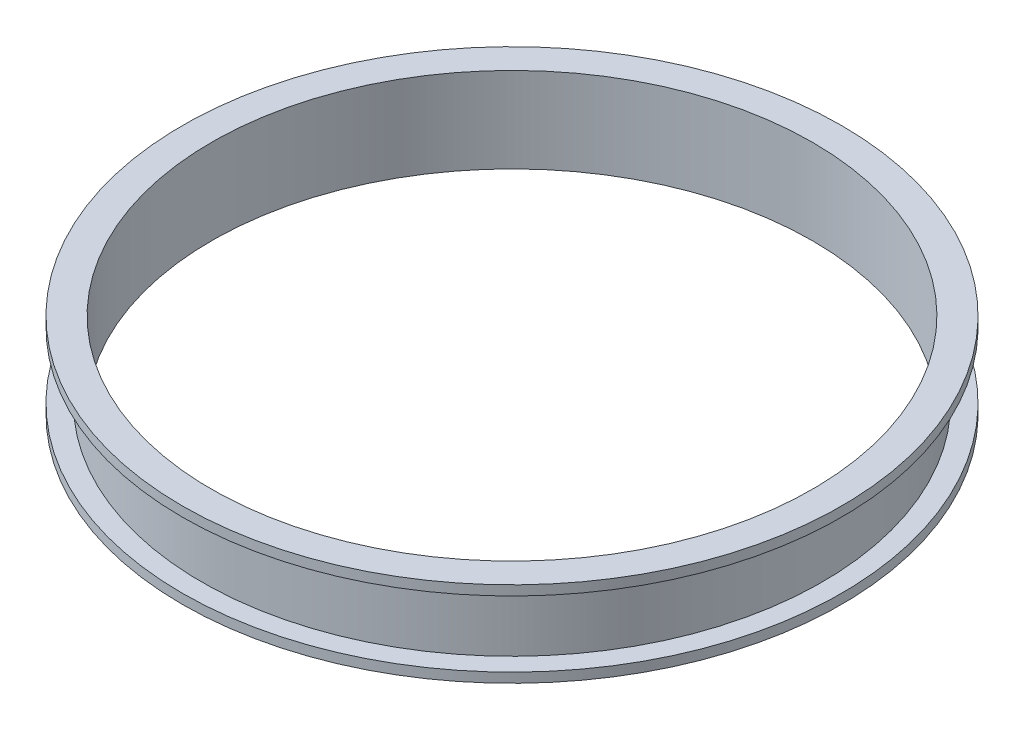
SolidWorks part; units mm, degrees
ref_plane "Front Plane" through (0, 0, 0) normal (0, 0, 1) x (1, 0, 0)
ref_plane "Top Plane" through (0, 0, 0) normal (0, 1, 0) x (1, 0, 0)
ref_plane "Right Plane" through (0, 0, 0) normal (1, 0, 0) x (0, 0, -1)
sketch "Sketch1" plane through (0, 0, 0) normal (0, 0, 1) x (1, 0, 0)
  line L0 (0, 0) -> (77.5, 0)
  line L1 (77.5, 0) -> (77.5, 19.5)
  line L2 (77.5, 19.5) -> (85, 19.5)
  line L3 (85, 19.5) -> (85, 17)
  line L4 (85, 17) -> (80, 17)
  line L5 (80, 17) -> (80, 0)
  line L6 (80, 0) -> (85, 0)
  line L7 (85, 0) -> (85, -2.5)
  line L8 (85, -2.5) -> (0, -2.5)
  line L9 (0, -2.5) -> (0, 0)
  dimension "D1" = 2.5
  dimension "D2" = 2.5
  dimension "D3" = 2.5
  dimension "D4" = 5
  dimension "D5" = 5
  dimension "D6" = 77.5
  dimension "D7" = 17
revolve "Revolve1" add sketch "Sketch1" angle 360 about L9
sketch "Sketch2" plane through (0, 0, 0) normal (0, 1, 0) x (1, 0, 0)
  circle A0 centre (0, 0) radius 77.5
  dimension "D1" = 155
extrude "Cut-Extrude1" cut sketch "Sketch2" against normal up to next
